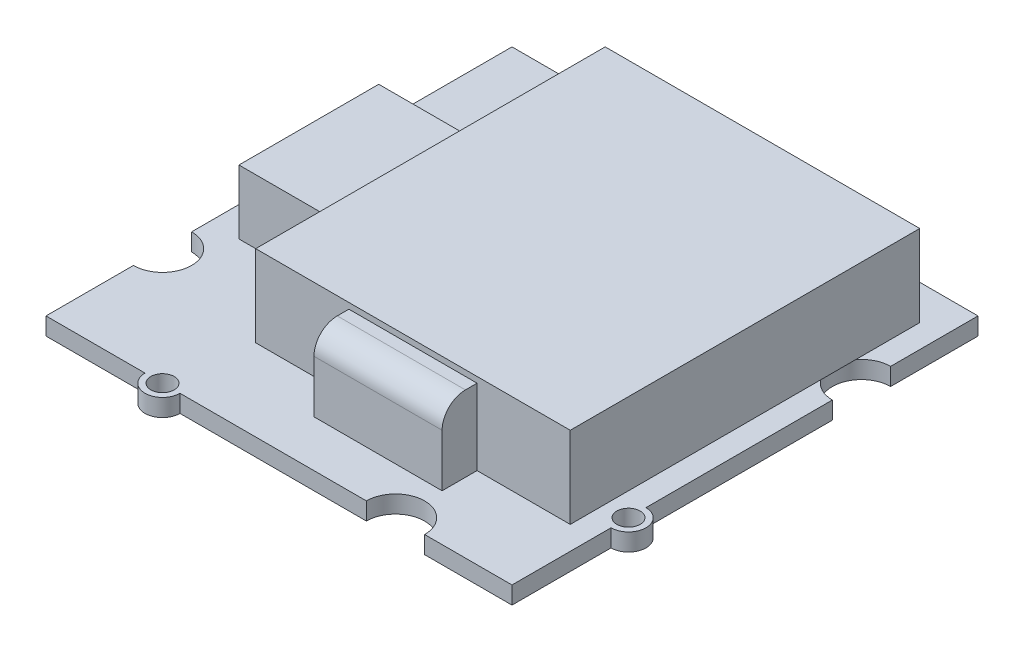
SolidWorks part; units mm, degrees
ref_plane "Front Plane" through (0, 0, 0) normal (0, 0, 1) x (1, 0, 0)
ref_plane "Top Plane" through (0, 0, 0) normal (0, 1, 0) x (1, 0, 0)
ref_plane "Right Plane" through (0, 0, 0) normal (1, 0, 0) x (0, 0, -1)
sketch "Sketch1" plane through (0, 0, 0) normal (0, 1, 0) x (1, 0, 0)
  line L1 (-20, 20) -> (20, 20)
  line L2 (-20, 20) -> (-20, -20)
  line L3 (-20, -20) -> (20, -20)
  line L4 (20, 20) -> (20, -20)
  line L5 (-20, 20) -> (20, -20) construction
  line L6 (-20, -20) -> (20, 20) construction
  point P0 (0, 0)
  dimension "D1" = 40
  dimension "D2" = 40
extrude "Boss-Extrude1" add sketch "Sketch1" along normal blind 1.5
sketch "Sketch2" plane through (0, 1.5, 0) normal (0, 1, 0) x (1, 0, 0)
  line L0 (-20, 20) -> (-20, -20) construction
  line L1 (20, 20) -> (-20, 20) construction
  line L2 (20, -20) -> (20, 20) construction
  line L3 (-20, -20) -> (20, -20) construction
  circle A0 centre (-20, 10) radius 1.5
  circle A1 centre (10, 20) radius 1.5
  circle A2 centre (20, -10) radius 1.5
  circle A3 centre (-10, -20) radius 1.5
  dimension "D1" = 3
  dimension "D2" = 3
  dimension "D3" = 3
  dimension "D4" = 3
  dimension "D5" = 10
  dimension "D6" = 10
  dimension "D7" = 10
  dimension "D8" = 10
extrude "Boss-Extrude2" add sketch "Sketch2" against normal blind 1.5
sketch "Sketch3" plane through (0, 1.5, 0) normal (0, 1, 0) x (1, 0, 0)
  line L0 (8.5, 20) -> (-20, 20) construction
  line L1 (20, -8.5) -> (20, 20) construction
  line L2 (-8.5, -20) -> (20, -20) construction
  line L3 (-20, 8.5) -> (-20, -20) construction
  line L4 (-20, -20) -> (-11.5, -20) construction
  line L5 (20, -20) -> (20, -11.5) construction
  line L6 (20, 20) -> (11.5, 20) construction
  line L7 (-20, 20) -> (-20, 11.5) construction
  circle A0 centre (-20, 10) radius 1
  circle A1 centre (10, 20) radius 1
  circle A2 centre (20, -10) radius 1
  circle A3 centre (-10, -20) radius 1
  circle A4 centre (-10, 20) radius 2.5
  circle A5 centre (20, 10) radius 2.5
  circle A6 centre (10, -20) radius 2.5
  circle A7 centre (-20, -10) radius 2.5
  dimension "D1" = 2
  dimension "D2" = 2
  dimension "D3" = 2
  dimension "D4" = 2
  dimension "D5" = 5
  dimension "D6" = 5
  dimension "D7" = 5
  dimension "D8" = 5
  dimension "D10" = 10
  dimension "D12" = 10
  dimension "D9" = 10
  dimension "D11" = 10
extrude "Cut-Extrude1" cut sketch "Sketch3" against normal blind 1.5
sketch "Sketch4" plane through (0, 1.5, 0) normal (0, 1, 0) x (1, 0, 0)
  line L0 (-12.5, 20) -> (-20, 20) construction
  line L1 (-17.4389, 6) -> (-9.4389, 6)
  line L2 (-17.4389, 6) -> (-17.4389, -6)
  line L3 (-17.4389, -6) -> (-9.4389, -6)
  line L4 (-9.4389, 6) -> (-9.4389, -6)
  line L5 (-17.4389, 6) -> (-9.4389, -6) construction
  line L6 (-17.4389, -6) -> (-9.4389, 6) construction
  line L7 (-20, -20) -> (-11.5, -20) construction
  point P0 (-13.4389, 0)
  dimension "D1" = 8
  dimension "D2" = 12
  dimension "D3" = 14
  dimension "D4" = 14
extrude "Boss-Extrude3" add sketch "Sketch4" along normal blind 5.5
sketch "Sketch5" plane through (0, 1.5, 0) normal (0, 1, 0) x (1, 0, 0)
  line L0 (8.5, 20) -> (-7.5, 20) construction
  line L1 (-9, 17) -> (18, 17)
  line L2 (-9, 17) -> (-9, -13)
  line L3 (-9, -13) -> (18, -13)
  line L4 (18, 17) -> (18, -13)
  line L5 (-9, 17) -> (18, -13) construction
  line L6 (-9, -13) -> (18, 17) construction
  line L7 (20, -8.5) -> (20, 7.5) construction
  point P0 (4.5, 2)
  dimension "D1" = 3
  dimension "D2" = 2
  dimension "D3" = 27
  dimension "D4" = 30
extrude "Boss-Extrude4" add sketch "Sketch5" along normal blind 7
sketch "Sketch6" plane through (0, 1.5, 0) normal (0, 1, 0) x (1, 0, 0)
  line L0 (-8.5, -20) -> (7.5, -20) construction
  line L1 (-1, -13) -> (10, -13)
  line L2 (-1, -13) -> (-1, -16)
  line L3 (-1, -16) -> (10, -16)
  line L4 (10, -13) -> (10, -16)
  line L5 (-1, -13) -> (10, -16) construction
  line L6 (-1, -16) -> (10, -13) construction
  line L7 (20, -20) -> (20, -11.5) construction
  point P0 (4.5, -14.5)
  dimension "D1" = 3
  dimension "D2" = 11
  dimension "D3" = 4
  dimension "D4" = 10
extrude "Boss-Extrude5" add sketch "Sketch6" along normal blind 6.5
fillet "Fillet1" radius 2 1 edges at (4.5, 8, 16)
